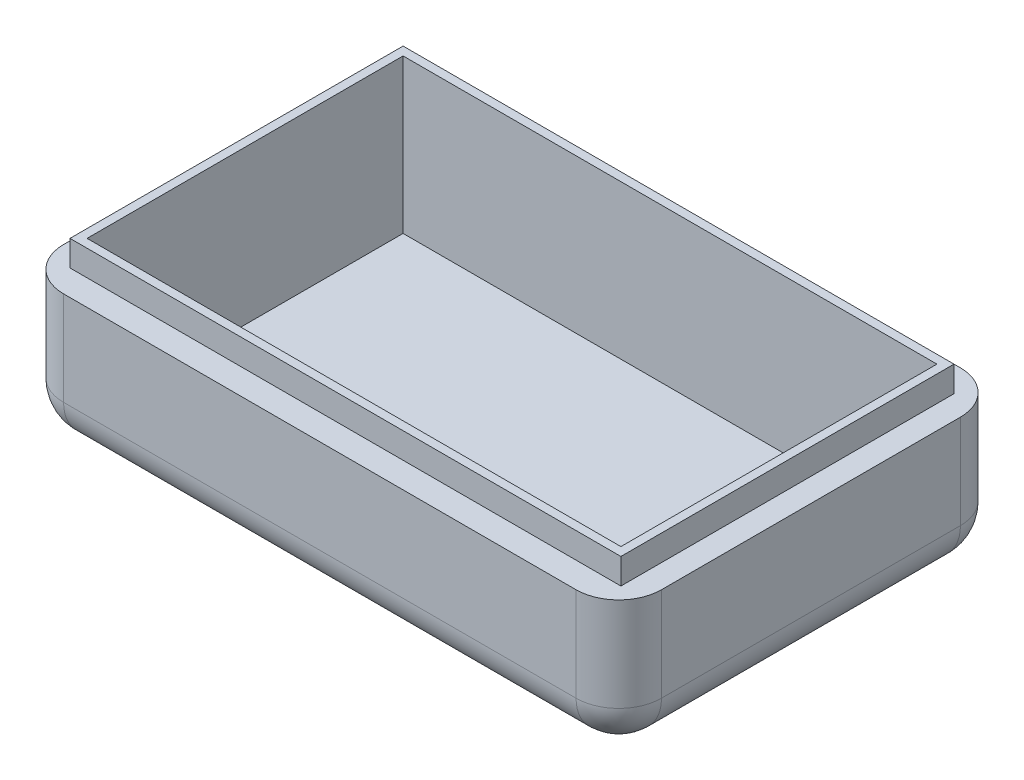
SolidWorks part; units mm, degrees
ref_plane "前视基准面" through (0, 0, 0) normal (0, 0, 1) x (1, 0, 0)
ref_plane "上视基准面" through (0, 0, 0) normal (0, 1, 0) x (1, 0, 0)
ref_plane "右视基准面" through (0, 0, 0) normal (1, 0, 0) x (0, 0, -1)
sketch "草图1" plane through (0, 0, 0) normal (0, 1, 0) x (1, 0, 0)
  line L1 (-32.25, 19.5) -> (32.25, 19.5)
  line L2 (-32.25, 19.5) -> (-32.25, -19.5)
  line L3 (-32.25, -19.5) -> (32.25, -19.5)
  line L4 (32.25, 19.5) -> (32.25, -19.5)
  line L5 (-32.25, 19.5) -> (32.25, -19.5) construction
  line L6 (-32.25, -19.5) -> (32.25, 19.5) construction
  line L7 (-31.25, 18.5) -> (31.25, 18.5)
  line L8 (-31.25, 18.5) -> (-31.25, -18.5)
  line L9 (-31.25, -18.5) -> (31.25, -18.5)
  line L10 (31.25, 18.5) -> (31.25, -18.5)
  point P0 (0, 0)
  dimension "D1" = 39
  dimension "D2" = 64.5
  dimension "D3" = 1
  dimension "D4" = 1
  dimension "D5" = 1
  dimension "D6" = 1
extrude "凸台-拉伸2" add sketch "草图1" along normal blind 3
sketch "草图2" plane through (0, 0, 0) normal (0, 1, 0) x (1, 0, 0)
  line L1 (-35, -22.5) -> (35, -22.5)
  line L2 (-35, -22.5) -> (-35, 22.5)
  line L3 (-35, 22.5) -> (35, 22.5)
  line L4 (35, -22.5) -> (35, 22.5)
  line L5 (-35, -22.5) -> (35, 22.5) construction
  line L6 (-35, 22.5) -> (35, -22.5) construction
  line L7 (-31.25, -18.5) -> (31.25, -18.5)
  line L8 (-31.25, -18.5) -> (-31.25, 18.5)
  line L9 (-31.25, 18.5) -> (31.25, 18.5)
  line L10 (31.25, -18.5) -> (31.25, 18.5)
  point P0 (0, 0)
  dimension "D1" = 45
  dimension "D2" = 70
extrude "凸台-拉伸3" add sketch "草图2" against normal blind 15
sketch "草图3" plane through (0, 0, 0) normal (0, 1, 0) x (1, 0, 0)
  line L1 (-35, -22.5) -> (35, -22.5)
  line L2 (-35, -22.5) -> (-35, 22.5)
  line L3 (-35, 22.5) -> (35, 22.5)
  line L4 (35, -22.5) -> (35, 22.5)
sketch "草图4" plane through (0, 0, 0) normal (0, 0, 1) x (1, 0, 0)
  line L1 (-35, -15) -> (35, -15)
  line L2 (-35, -15) -> (-35, -16)
  line L3 (-35, -16) -> (35, -16)
  line L4 (35, -15) -> (35, -16)
  dimension "D1" = 1
extrude "凸台-拉伸4" add sketch "草图4" along normal mid plane 45 contours L3 L4 L1 L2
fillet "圆角1" radius 5 4 edges at (35, -8, 22.5) (35, -8, -22.5) (-35, -8, 22.5) (-35, -8, -22.5)
fillet "圆角2" radius 5 8 edges at (-33.5355, -16, -21.0355) (-33.5355, -16, 21.0355) (33.5355, -16, 21.0355) (33.5355, -16, -21.0355) (35, -16, 0) (0, -16, -22.5) (-35, -16, 0) (0, -16, 22.5)
